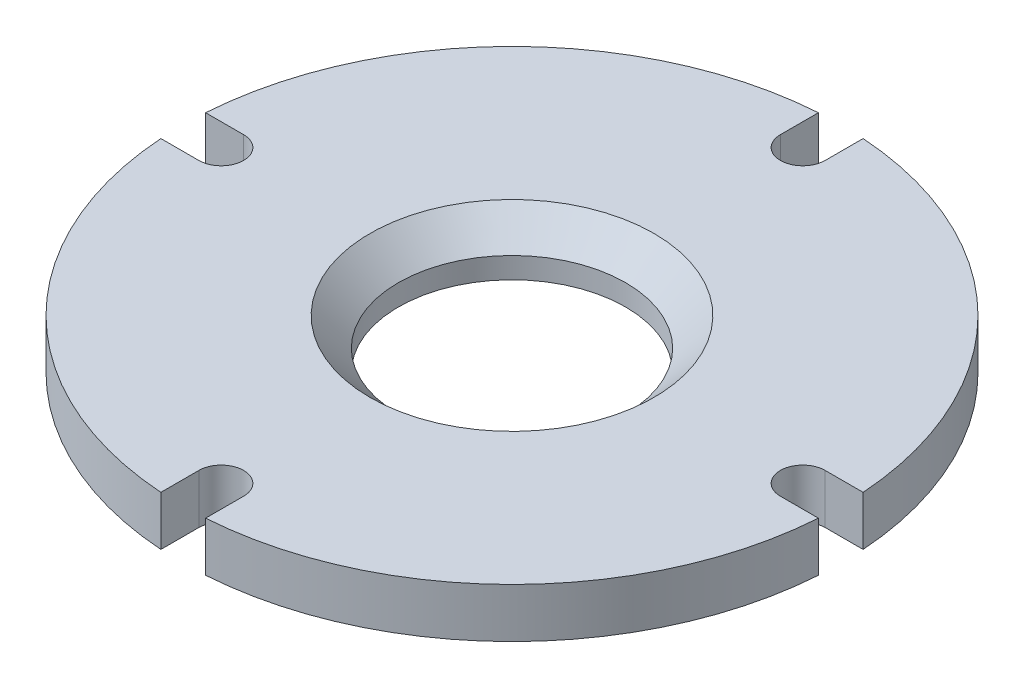
SolidWorks part; units mm, degrees
ref_plane "Front Plane" through (0, 0, 0) normal (0, 0, 1) x (1, 0, 0)
ref_plane "Top Plane" through (0, 0, 0) normal (0, 1, 0) x (1, 0, 0)
ref_plane "Right Plane" through (0, 0, 0) normal (1, 0, 0) x (0, 0, -1)
ref_plane "Plane1" through (0, 0, 0) normal (0, 0, -1) x (-1, 0, 0)
sketch "Sketch1" plane through (0, 0, 0) normal (0, 0, -1) x (-1, 0, 0)
  line L0 (-36.83, -5.5298) -> (0, -5.5298)
  line L1 (0, -5.5298) -> (0, 0)
  line L2 (0, 0) -> (-36.83, 0)
  line L3 (-36.83, 0) -> (-36.83, -5.5298)
  line L4 (0, -5.5298) -> (0, 0) construction
  dimension "D1" = 36.83
  dimension "D2" = 0
revolve "Revolve1" add sketch "Sketch1" angle 360 about L4
sketch "Sketch5" plane through (0, -5.5298, 0) normal (0, -1, 0) x (1, 0, 0)
  circle A0 centre (0, 0) radius 27.5
  dimension "D1" = 55
extrude "Boss-Extrude1" add sketch "Sketch5" along normal blind 0.001
sketch "Sketch6" plane through (0, -5.5308, 0) normal (0, -1, 0) x (1, 0, 0)
  circle A0 centre (0, 0) radius 15.8
extrude "Boss-Extrude2" [suppressed] add sketch "Sketch6" along normal blind 20
sketch "Sketch7" [suppressed] plane through (0, -32.5, 0) normal (0, -1, 0) x (1, 0, 0)
  line L0 (7.0012, -3.6054) -> (10.6066, 0)
  line L1 (10.6066, 0) -> (7.0012, 3.6054)
  line L2 (3.6054, 7.0012) -> (0, 10.6066)
  line L3 (0, 10.6066) -> (-3.6054, 7.0012)
  line L4 (-7.0012, 3.6054) -> (-10.6066, 0)
  line L5 (-10.6066, 0) -> (-7.0012, -3.6054)
  line L6 (-3.6054, -7.0012) -> (0, -10.6066)
  line L7 (0, -10.6066) -> (3.6054, -7.0012)
  arc A0 (3.8947, -6.8445) -> (6.8445, -3.8947) centre (4.773, -4.773) ccw
  arc A1 (6.8445, -3.8947) -> (7.0012, -3.6054) centre (0, 0) ccw
  arc A2 (7.0012, 3.6054) -> (6.8445, 3.8947) centre (0, 0) ccw
  arc A3 (6.8445, 3.8947) -> (3.8947, 6.8445) centre (4.773, 4.773) ccw
  arc A4 (3.8947, 6.8445) -> (3.6054, 7.0012) centre (0, 0) ccw
  arc A5 (-3.6054, 7.0012) -> (-3.8947, 6.8445) centre (0, 0) ccw
  arc A6 (-3.8947, 6.8445) -> (-6.8445, 3.8947) centre (-4.773, 4.773) ccw
  arc A7 (-6.8445, 3.8947) -> (-7.0012, 3.6054) centre (0, 0) ccw
  arc A8 (-7.0012, -3.6054) -> (-6.8445, -3.8947) centre (0, 0) ccw
  arc A9 (-6.8445, -3.8947) -> (-3.8947, -6.8445) centre (-4.773, -4.773) ccw
  arc A10 (-3.8947, -6.8445) -> (-3.6054, -7.0012) centre (0, 0) ccw
  arc A11 (3.6054, -7.0012) -> (3.8947, -6.8445) centre (0, 0) ccw
extrude "Cut-Extrude4" [suppressed] cut sketch "Sketch7" against normal blind 20
hole_wizard "M12 Clearance Hole1" [suppressed] positions "Sketch9" profile "Sketch8" hole size "M12" standard "ANSI Metric"
sketch "Sketch9" [suppressed] plane through (0, -12.5, 0) normal (0, -1, 0) x (-1, 0, 0)
  point P0 (0, 0)
sketch "Sketch8" plane through (0, -12.5, 0) normal (1, 0, 0) x (0, 0, -1)
  line L0 (0, 0) -> (0, 12.5)
  line L1 (0, 12.5) -> (6.5454, 12.5)
  line L2 (6.5454, 12.5) -> (6.5454, 0)
  line L5 (6.5454, 0) -> (0, 0)
  line L11 (0, -6.35) -> (0, 107.95) construction
  dimension "Thru Hole Dia." = 13.0907
  dimension "Thru Hole Depth" = 12.5
sketch "Sketch10" plane through (0, 0, 0) normal (0, 0, 1) x (1, 0, 0)
  line L0 (5.5454, -11.5) -> (0, -11.5)
  line L1 (0, -11.5) -> (0, -12.5)
  line L2 (0, -12.5) -> (5.5454, -12.5)
  line L3 (5.5454, -12.5) -> (5.5454, -11.5)
  line L4 (0, -11.5) -> (0, -12.5) construction
revolve "Revolve2" [suppressed] add sketch "Sketch10" angle 360 about L4
sketch "Sketch11" plane through (0, 0, 0) normal (0, 0, 1) x (1, 0, 0)
  line L0 (25, 4.5) -> (0, 4.5)
  line L1 (0, 4.5) -> (0, 0)
  line L2 (0, 0) -> (25, 0)
  line L3 (25, 0) -> (25, 4.5)
  line L4 (0, 4.5) -> (0, 0) construction
revolve "Revolve3" [suppressed] add sketch "Sketch11" angle 360 about L4
hole_wizard "#4-40 Tapped Hole1" positions "Sketch13" profile "Sketch12" tap size "#4-40" standard "ANSI Inch"
sketch "Sketch13" plane through (0, -5.5308, 0) normal (0, -1, 0) x (-1, 0, 0)
  line L0 (0, 0) -> (21.8996, -21.8996) construction
  line L4 (-3.9638, 0) -> (18.6967, 0) construction
  point P2 (14.6018, -14.6018)
  dimension "D1" = 20.65
  dimension "D2" = 45
sketch "Sketch12" plane through (-14.6018, -5.5308, 14.6018) normal (1, 0, 0) x (0, 0, -1)
  line L0 (0, 0) -> (0, 3.9812)
  line L1 (0, 3.9812) -> (1.1303, 3.302)
  line L2 (1.1303, 3.302) -> (1.1303, 0)
  line L5 (1.1303, 0) -> (0, 0)
  line L10 (0, 3.9812) -> (-1.1303, 3.302) construction
  line L11 (0, -6.35) -> (0, 107.95) construction
  dimension "Tap Drill Dia." = 2.2606
  dimension "Tap Drill Depth" = 3.302
  dimension "Drill Angle" = 118
sketch "Sketch19" plane through (0, -5.5308, 0) normal (0, -1, 0) x (1, 0, 0)
  circle A0 centre (0, 0) radius 12.7
  dimension "D1" = 25.4
extrude "Cut-Extrude6" cut sketch "Sketch19" against normal through all
pattern_circular "CirPattern1" count 4 over 360 about axis through (0, 0, 0) along (0, 1, 0) of "#4-40 Tapped Hole1"
sketch "Sketch20" plane through (0, -5.5298, 0) normal (0, -1, 0) x (-1, 0, 0)
  line L0 (0, -32.5) -> (0, -42.5) construction
  line L1 (2.5, -32.5) -> (2.5, -42.5)
  line L2 (-2.5, -32.5) -> (-2.5, -42.5)
  arc A0 (2.5, -32.5) -> (-2.5, -32.5) centre (0, -32.5) ccw
  arc A1 (-2.5, -42.5) -> (2.5, -42.5) centre (0, -42.5) ccw
  point P3 (0, -37.5)
  dimension "D2" = 2.5
  dimension "D1" = 32.5
  dimension "D3" = 10
extrude "Cut-Extrude7" cut sketch "Sketch20" against normal through all
pattern_circular "CirPattern2" count 4 over 360 about axis through (0, 0, 0) along (0, 1, 0) of "Cut-Extrude7"
sketch "Sketch21" plane through (0, -5.5308, 0) normal (0, -1, 0) x (1, 0, 0)
  line L0 (0, 0) -> (-43.0564, 0) construction
  line L1 (0, 0) -> (-31.3147, 31.3147) construction
  circle A0 centre (-6.0811, 6.0811) radius 4.75
  dimension "D1" = 9.5
  dimension "D2" = 45
  dimension "D3" = 8.6
extrude "Cut-Extrude8" [suppressed] cut sketch "Sketch21" against normal offset from surface (3.501 mm away) 2
pattern_circular "CirPattern3" [suppressed] count 4 over 360
sketch "Sketch22" plane through (0, -5.5308, 0) normal (0, -1, 0) x (-1, 0, 0)
  circle A0 centre (8.6, 0) radius 4.75
  dimension "D1" = 9.5
  dimension "D2" = 8.6
extrude "Cut-Extrude9" [suppressed] cut sketch "Sketch22" against normal through all
pattern_circular "CirPattern4" [suppressed] count 4 over 360
sketch "Sketch23" [suppressed] plane through (0, -2, 0) normal (0, -1, 0) x (1, 0, 0)
  circle A0 centre (0, 0) radius 10
  dimension "D1" = 20
extrude "Cut-Extrude10" [suppressed] cut sketch "Sketch23" against normal through all
sketch "Sketch24" plane through (0, 0, 0) normal (0, 1, 0) x (1, 0, 0)
  circle A0 centre (0, 0) radius 13.97
  circle A1 centre (0, 0) radius 16.2052
  dimension "D1" = 27.94
  dimension "D2" = 2.2352
extrude "Cut-Extrude11" [suppressed] cut sketch "Sketch24" against normal blind 1.3208
sketch "Sketch25" plane through (0, 0, 0) normal (0, 1, 0) x (1, 0, 0)
  circle A0 centre (0, 0) radius 26.67
  circle A1 centre (0, 0) radius 28.9052
  dimension "D1" = 53.34
  dimension "D2" = 2.2352
extrude "Cut-Extrude12" [suppressed] cut sketch "Sketch25" against normal blind 1.3208
hole_wizard "M2 Clearance Hole1" [suppressed] positions "Sketch15" profile "Sketch14" hole size "M2" standard "ANSI Metric"
sketch "Sketch15" [suppressed] plane through (0, 4.5, 0) normal (0, 1, 0) x (1, 0, 0)
  point P0 (0, -10)
  point P1 (10, 0)
  point P2 (0, 10)
  point P3 (-10, 0)
sketch "Sketch14" plane through (0, 4.5, 10) normal (1, 0, 0) x (0, 0, 1)
  line L0 (0, 0) -> (0, 3.6792)
  line L1 (0, 3.6792) -> (1.1303, 3)
  line L2 (1.1303, 3) -> (1.1303, 0)
  line L5 (1.1303, 0) -> (0, 0)
  line L10 (0, 3.6792) -> (-1.1303, 3) construction
  line L11 (0, -6.35) -> (0, 107.95) construction
  dimension "Hole Dia." = 2.2606
  dimension "Hole Depth" = 3
  dimension "Drill Angle" = 118
fillet "Fillet1" [suppressed] radius 2.5
sketch "Sketch18" [suppressed] plane through (0, -12.5, 0) normal (0, -1, 0) x (1, 0, 0)
  circle A0 centre (0, 0) radius 5
  dimension "D1" = 10
extrude "Cut-Extrude5" [suppressed] cut sketch "Sketch18" against normal through all
sketch "Sketch26" plane through (0, -5.5308, 0) normal (0, -1, 0) x (1, 0, 0)
  circle A0 centre (0, 0) radius 27.5
extrude "Cut-Extrude13" [suppressed] cut sketch "Sketch26" against normal up to surface (3.501 mm away)
sketch "Sketch27" [suppressed] plane through (0, -2, 0) normal (0, -1, 0) x (1, 0, 0)
  circle A0 centre (0, 0) radius 13.97
  circle A1 centre (0, 0) radius 16.2052
  dimension "D1" = 27.94
  dimension "D2" = 2.2352
extrude "Cut-Extrude15" [suppressed] cut sketch "Sketch27" against normal blind 1.27
chamfer "Chamfer1" distance 3.175 angle 45 1 edges at (0, 0, -12.7)
sketch "Sketch28" plane through (0, -5.5308, 0) normal (0, -1, 0) x (1, 0, 0)
  circle A0 centre (0, 0) radius 13.97
  circle A1 centre (0, 0) radius 16.2052
  dimension "D1" = 27.94
  dimension "D2" = 2.2352
extrude "Cut-Extrude17" cut sketch "Sketch28" against normal blind 1.3208
